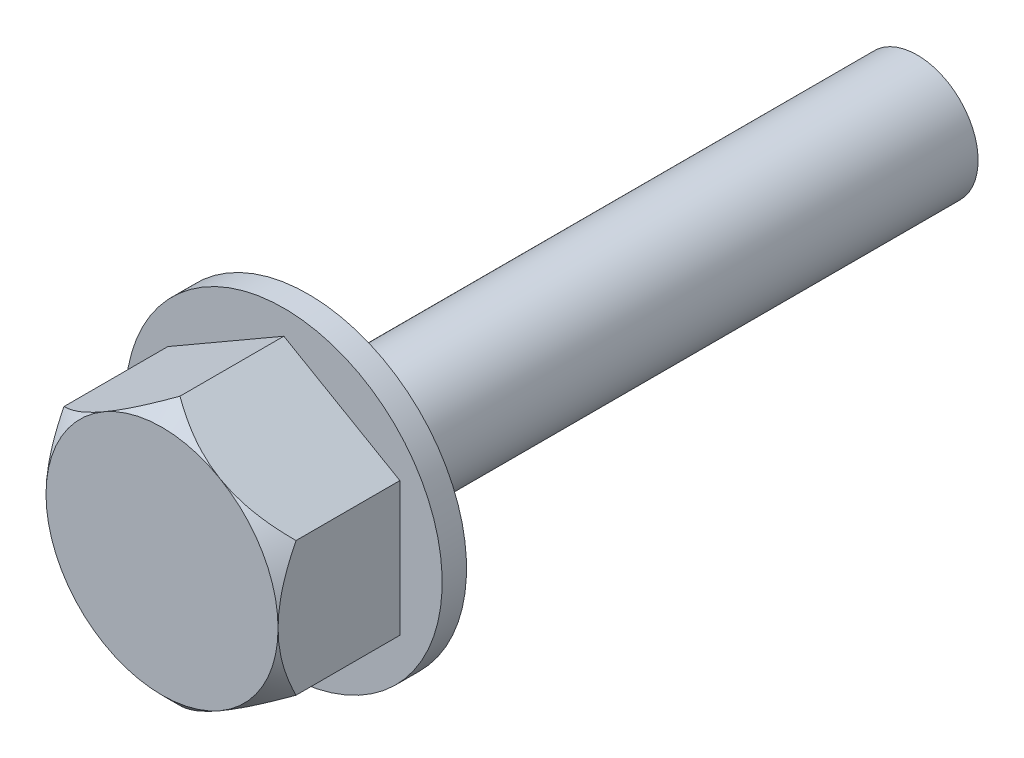
SolidWorks part; units mm, degrees
ref_plane "Front Plane" through (0, 0, 0) normal (0, 0, 1) x (1, 0, 0)
ref_plane "Top Plane" through (0, 0, 0) normal (0, 1, 0) x (1, 0, 0)
ref_plane "Right Plane" through (0, 0, 0) normal (1, 0, 0) x (0, 0, -1)
sketch "Sketch1" plane through (0, 0, 0) normal (0, 0, 1) x (1, 0, 0)
  line L1 (0, -5.5) -> (4.7631, -2.75)
  line L2 (4.7631, -2.75) -> (4.7631, 2.75)
  line L3 (4.7631, 2.75) -> (0, 5.5)
  line L4 (0, 5.5) -> (-4.7631, 2.75)
  line L5 (-4.7631, 2.75) -> (-4.7631, -2.75)
  line L6 (-4.7631, -2.75) -> (0, -5.5)
  circle A0 centre (0, 0) radius 4.7631 construction
  dimension "D1" = 11
extrude "Boss-Extrude1" add sketch "Sketch1" against normal blind 5
sketch "Sketch2" plane through (0, 0, 0) normal (0, 0, 1) x (1, 0, 0)
  circle A0 centre (0, 0) radius 4.7631
extrude "Cut-Extrude2" cut sketch "Sketch2" against normal blind 5 draft 45 flip side to cut
sketch "Sketch5" plane through (0, 0, -5) normal (0, 0, -1) x (-1, 0, 0)
  circle A0 centre (0, 0) radius 6.5
  dimension "D1" = 13
extrude "Boss-Extrude2" add sketch "Sketch5" along normal blind 1
sketch "Sketch6" plane through (0, 0, -6) normal (0, 0, -1) x (-1, 0, 0)
  circle A0 centre (0, 0) radius 2.5
  dimension "D1" = 5
extrude "Boss-Extrude3" add sketch "Sketch6" along normal blind 25
